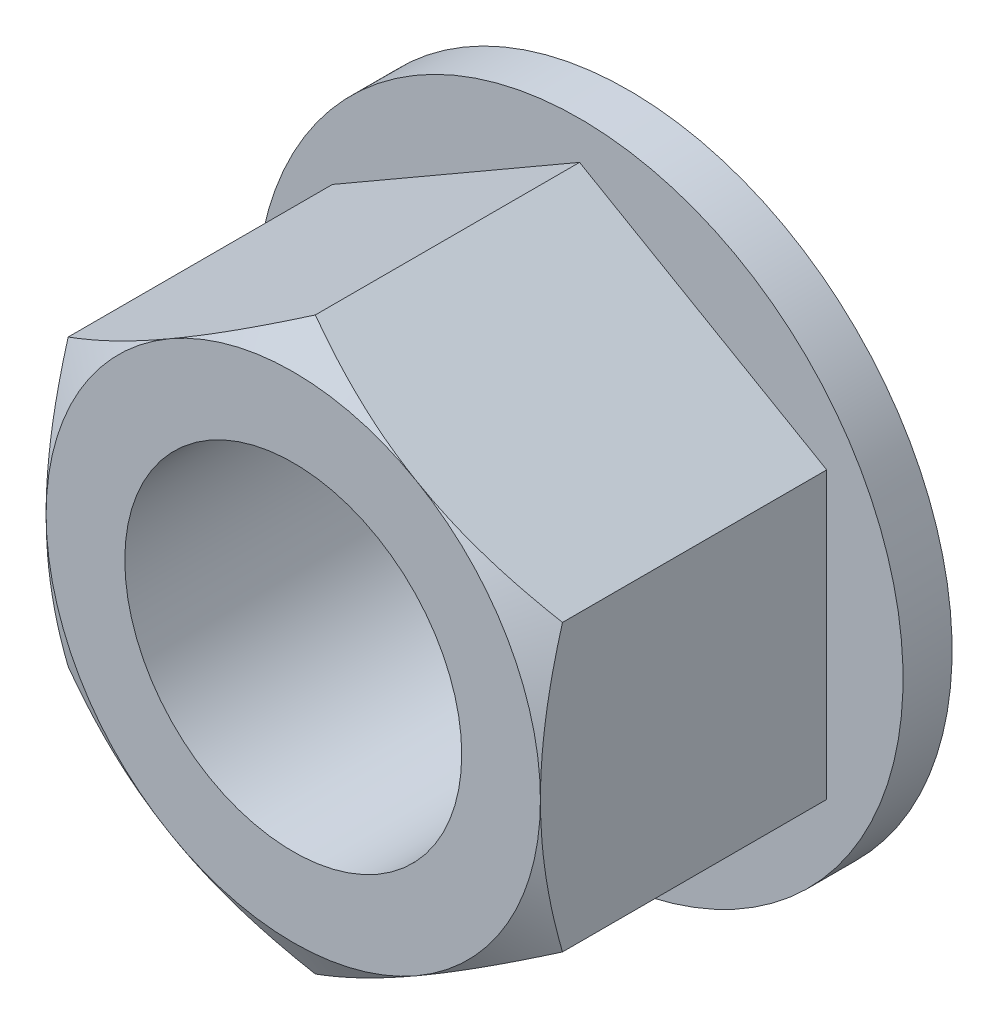
SolidWorks part; units mm, degrees
material "6061-T6 (SS)"
ref_plane "Front" through (0, 0, 0) normal (0, 0, 1) x (1, 0, 0)
ref_plane "Top" through (0, 0, 0) normal (0, 1, 0) x (1, 0, 0)
ref_plane "Right" through (0, 0, 0) normal (1, 0, 0) x (0, 0, -1)
sketch "Sketch1" plane through (0, 0, 0) normal (0, 0, 1) x (1, 0, 0)
  line L1 (3.9687, -2.2914) -> (3.9687, 2.2914)
  line L2 (3.9687, 2.2914) -> (0, 4.5827)
  line L3 (0, 4.5827) -> (-3.9688, 2.2914)
  line L4 (-3.9688, 2.2914) -> (-3.9688, -2.2914)
  line L5 (-3.9688, -2.2914) -> (0, -4.5827)
  line L6 (0, -4.5827) -> (3.9687, -2.2914)
  circle A0 centre (0, 0) radius 3.9688 construction
  dimension "Hex" = 7.9375
extrude "Extrude1" add sketch "Sketch1" along normal mid plane 5.3848
sketch "Sketch2" plane through (0, 0, 2.6924) normal (0, 0, 1) x (1, 0, 0)
  circle A0 centre (0, 0) radius 3.9688 construction
  circle A5 centre (0, 0) radius 3.9688
extrude "Cut-Extrude1" cut sketch "Sketch2" against normal through all draft 60 flip side to cut
sketch "Sketch17" plane through (0, 0, -2.6924) normal (0, 0, -1) x (-1, 0, 0)
  circle A0 centre (0, 0) radius 5.1943
  dimension "Flange OD" = 10.3886
extrude "Extrude3" add sketch "Sketch17" against normal blind 0.7874
hole_wizard "1/4-28 Tapped Hole1" positions "Sketch21" profile "Sketch20" tap size "1/4-28" standard "ANSI Inch" end condition through all
sketch "Sketch21" plane through (0, 0, 2.6924) normal (0, 0, 1) x (1, 0, 0)
  point P0 (0, 0)
cosmetic thread "Hole Thread1" parameters "D2"=6.35
sketch "Sketch20" plane through (0, 0, 2.6924) normal (1, 0, 0) x (0, -1, 0)
  line L0 (0, 0) -> (0, 5.3848)
  line L1 (0, 5.3848) -> (2.7051, 5.3848)
  line L2 (2.7051, 5.3848) -> (2.7051, 0)
  line L5 (2.7051, 0) -> (0, 0)
  line L11 (0, -6.35) -> (0, 107.95) construction
  dimension "Thru Tap Drill Dia." = 5.4102
  dimension "Thru Tap Drill Depth" = 5.3848
